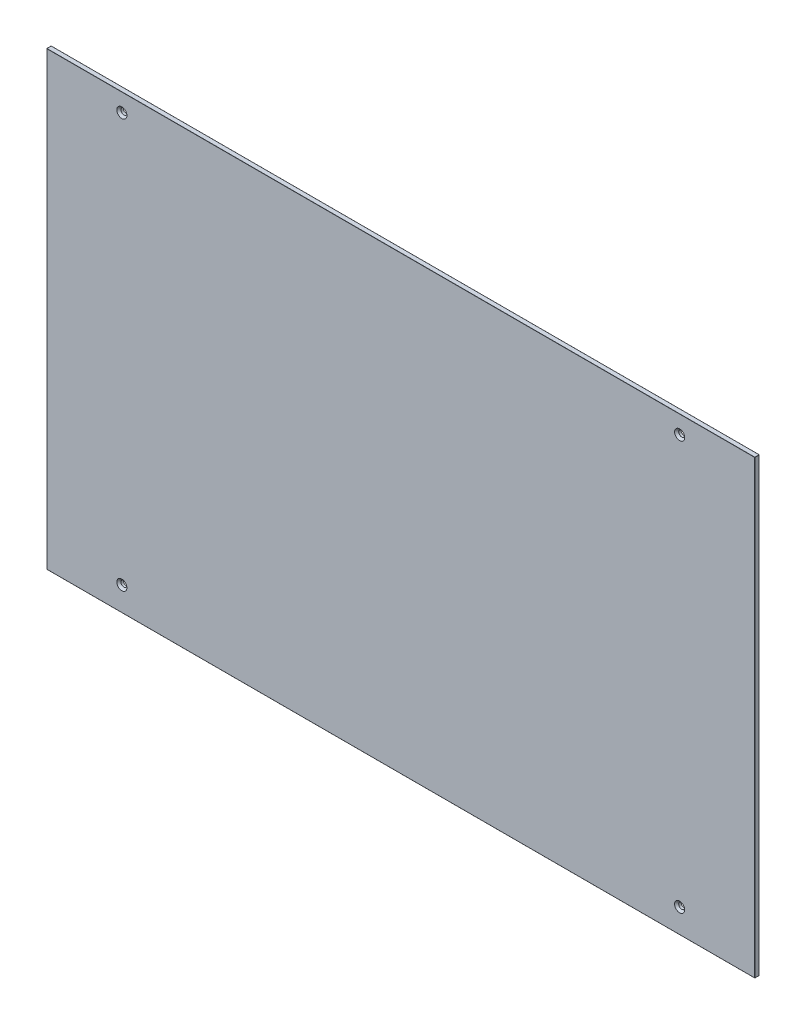
SolidWorks part; units mm, degrees
material "Glass"
ref_plane "Front Plane" through (0, 0, 0) normal (0, 0, 1) x (1, 0, 0)
ref_plane "Top Plane" through (0, 0, 0) normal (0, 1, 0) x (1, 0, 0)
ref_plane "Right Plane" through (0, 0, 0) normal (1, 0, 0) x (0, 0, -1)
sketch "Sketch1" plane through (0, 0, 0) normal (0, 0, 1) x (1, 0, 0)
  line L1 (-471, -300) -> (471, -300)
  line L2 (-471, -300) -> (-471, 300)
  line L3 (-471, 300) -> (471, 300)
  line L4 (471, -300) -> (471, 300)
  line L5 (-471, -300) -> (471, 300) construction
  line L6 (-471, 300) -> (471, -300) construction
  point P0 (0, 0)
  dimension "Largura" = 942
  dimension "Altura" = 600
extrude "Boss-Extrude1" add sketch "Sketch1" along normal blind 6
sketch "Sketch2" plane through (0, 0, 6) normal (0, 0, 1) x (1, 0, 0)
  line L0 (-471, 300) -> (-471, -300) construction
  line L1 (471, -300) -> (471, 300) construction
  line L2 (471, 300) -> (-471, 300) construction
  line L3 (-471, -300) -> (471, -300) construction
  circle A0 centre (-371, 276) radius 4
  circle A1 centre (371, 276) radius 4
  circle A2 centre (371, -268) radius 4
  circle A3 centre (-371, -268) radius 4
  dimension "D1" = 8
  dimension "D2" = 100
  dimension "D3" = 100
  dimension "D4" = 24
  dimension "D5" = 32
extrude "Cut-Extrude1" cut sketch "Sketch2" against normal through all
chamfer "Chamfer1" distance 2.75 angle 45 4 edges at (-367, -268, 6) (375, -268, 6) (375, 276, 6) (-367, 276, 6)
fillet "Fillet1" radius 0.2 12 edges at (0, -300, 0) (471, 0, 0) (471, -300, 3) (0, -300, 6) (471, 0, 6) (471, 300, 3) (-471, -300, 3) (0, 300, 0) (-471, 0, 0) (0, 300, 6) (-471, 300, 3) (-471, 0, 6)
